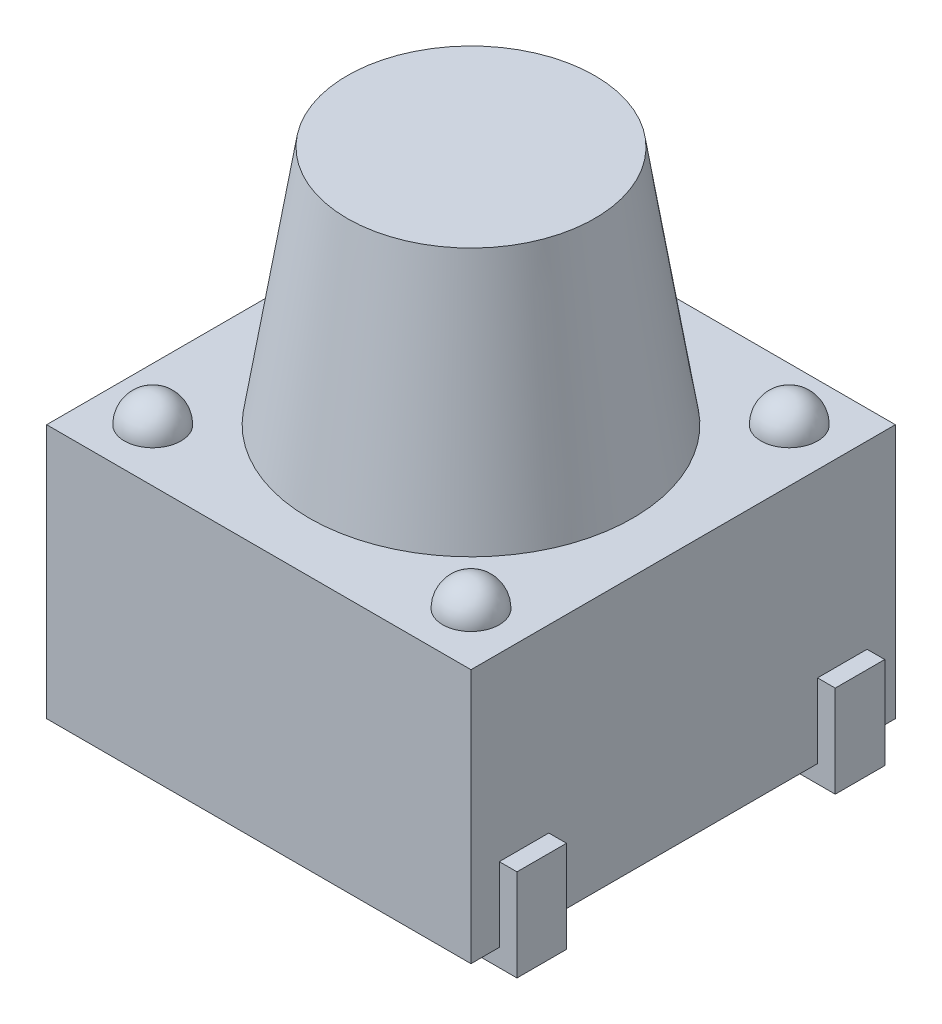
SolidWorks part; units mm, degrees
ref_plane "Front" through (0, 0, 0) normal (0, 0, 1) x (1, 0, 0)
ref_plane "Top" through (0, 0, 0) normal (0, 1, 0) x (1, 0, 0)
ref_plane "Right" through (0, 0, 0) normal (1, 0, 0) x (0, 0, -1)
sketch "Sketch1" plane through (0, 0, 0) normal (0, 1, 0) x (1, 0, 0)
  line L0 (3, 3) -> (-3, -3) construction
  line L1 (-3, 3) -> (3, 3)
  line L2 (-3, 3) -> (-3, -3)
  line L3 (-3, -3) -> (3, -3)
  line L4 (3, 3) -> (3, -3)
  dimension "D1" = 6
  dimension "D2" = 6
extrude "Extrude1" add sketch "Sketch1" along normal blind 3.6
ref_plane "Plane1" through (0, 0, 2.25) normal (0, 0, 1) x (1, 0, 0)
sketch "Sketch2" plane through (0, 0, 2.25) normal (0, 0, 1) x (1, 0, 0)
  line L0 (-3, 3.6) -> (3, 3.6) construction
  line L1 (0, 0) -> (0, 3.6) construction
  line L2 (-3, 0) -> (3, 0) construction
  line L3 (-2.25, 4.7074) -> (-2.25, 3.0312) construction
  line L4 (-2.25, 3.6) -> (-1.85, 3.6)
  line L5 (-2.25, 3.6) -> (-2.25, 4)
  arc A0 (1.85, 3.6) -> (2.65, 3.6) centre (2.25, 3.6) cw construction
  arc A1 (-2.25, 4) -> (-1.85, 3.6) centre (-2.25, 3.6) cw
  point P12 (2.25, 4)
  dimension "D3" = 0.4
  dimension "D1" = 4.5
  dimension "D2" = 2.25
  dimension "D4" = 0.4
revolve "Revolve1" add sketch "Sketch2" angle 360 about L3
mirror "Mirror1" about plane through (0, 0, 0) normal (0, 0, 1) of "Revolve1"
mirror "Mirror2" about plane through (0, 0, 0) normal (1, 0, 0) of "Mirror1", "Revolve1"
sketch "Sketch3" plane through (0, 0, 0) normal (0, 0, 1) x (1, 0, 0)
  line L0 (-2.2885, 3.6) -> (-1.75, 7)
  line L1 (-1.75, 7) -> (0, 7)
  line L2 (0, 7) -> (0, 0) construction
  line L3 (-2.2885, 3.6) -> (0, 3.6)
  line L4 (-3, 3.6) -> (3, 3.6) construction
  line L5 (0, 3.6) -> (0, 7)
  line L6 (-3, 0) -> (3, 0) construction
  dimension "D1" = 7
  dimension "D2" = 1.75
  dimension "D3" = 81
revolve "Revolve2" add sketch "Sketch3" angle 360 about L2
sketch "Sketch5" plane through (0, 0, 2.25) normal (0, 0, 1) x (1, 0, 0)
  line L0 (-3, 1.05) -> (-3.25, 1.05)
  line L1 (-3, 3.6) -> (-3, 0) construction
  line L2 (-3, 1.05) -> (-3, 0)
  line L3 (-3, 0) -> (-2.2154, 0)
  line L4 (-3.25, 1.05) -> (-3.25, -0.25)
  line L5 (-2.2154, 0) -> (-2.2154, -0.25)
  line L6 (-2.2154, -0.25) -> (-3.25, -0.25)
  line L7 (-3, 0) -> (3, 0) construction
  line L8 (0, 0) -> (0, 14.1618) construction
  dimension "D2" = 0.25
  dimension "D6" = 0.25
  dimension "D1" = 1.3
extrude "Extrude2" add sketch "Sketch5" along normal mid plane 0.7
mirror "Mirror3" about plane through (0, 0, 0) normal (0, 0, 1) of "Extrude2"
mirror "Mirror4" about plane through (0, 0, 0) normal (1, 0, 0) of "Mirror3", "Extrude2"
equation "\"D2@Sketch2\" = \"D1@Sketch2\"/2"
